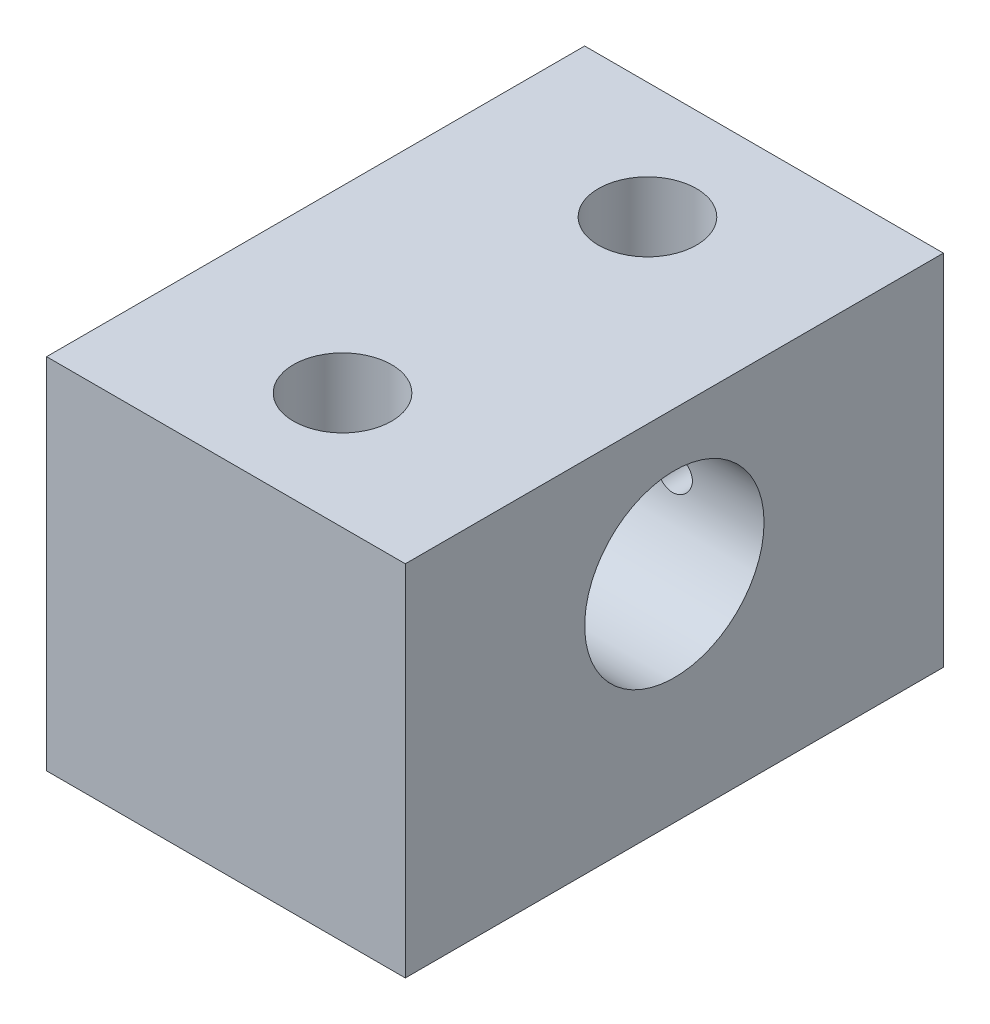
SolidWorks part; units mm, degrees
material "6061-T6 (SS)"
ref_plane "Front Plane" through (0, 0, 0) normal (0, 0, 1) x (1, 0, 0)
ref_plane "Top Plane" through (0, 0, 0) normal (0, 1, 0) x (1, 0, 0)
ref_plane "Right Plane" through (0, 0, 0) normal (1, 0, 0) x (0, 0, -1)
sketch "Sketch1" plane through (0, 0, 0) normal (0, 0, 1) x (1, 0, 0)
  line L1 (-25.4, -25.4) -> (25.4, -25.4)
  line L2 (-25.4, -25.4) -> (-25.4, 25.4)
  line L3 (-25.4, 25.4) -> (25.4, 25.4)
  line L4 (25.4, -25.4) -> (25.4, 25.4)
  line L5 (-25.4, -25.4) -> (25.4, 25.4) construction
  line L6 (-25.4, 25.4) -> (25.4, -25.4) construction
  point P0 (0, 0)
  dimension "D1" = 50.8
  dimension "D2" = 50.8
extrude "Extrude1" add sketch "Sketch1" along normal mid plane 76.2
sketch "Sketch2" plane through (25.4, 0, 0) normal (1, 0, 0) x (0, 0, -1)
  line L0 (38.1, 5.08) -> (0, 5.08) construction
  line L1 (-38.1, -25.4) -> (38.1, -25.4) construction
  line L2 (38.1, -25.4) -> (38.1, 25.4) construction
  line L3 (0, 27.94) -> (0, -27.94) construction
  circle A0 centre (0, 5.08) radius 12.7
  dimension "D2" = 25.4
  dimension "D3" = 30.48
extrude "Extrude2" cut sketch "Sketch2" against normal through all
sketch "Sketch3" plane through (0, 25.4, 0) normal (0, 1, 0) x (1, 0, 0)
  line L0 (0, 38.1) -> (0, -21.59) construction
  line L1 (25.4, 38.1) -> (-25.4, 38.1) construction
  line L2 (0, -21.59) -> (0, -38.1) construction
  line L3 (25.4, -38.1) -> (-25.4, -38.1) construction
  dimension "D1" = 16.51
hole_wizard "1/2 Clearance Hole1" positions "3DSketch1" profile "Sketch5" hole size "1/2" standard "Ansi Inch" end condition through all
sketch3d "3DSketch1"
  point P0 (0, 25.4, 21.59)
sketch "Sketch5" plane through (0, 25.4, 21.59) normal (1, 0, 0) x (0, 0, 1)
  line L0 (0, 0) -> (0, 50.8)
  line L1 (0, 50.8) -> (6.9456, 50.8)
  line L2 (6.9456, 50.8) -> (6.9456, 0)
  line L5 (6.9456, 0) -> (0, 0)
  line L11 (0, -6.35) -> (0, 107.95) construction
  dimension "Thru Hole Dia." = 13.8913
  dimension "Thru Hole Depth" = 50.8
mirror "Mirror1" about plane through (0, 0, 0) normal (0, 0, 1) of "1/2 Clearance Hole1"
sketch "Sketch6" plane through (0, 0, -38.1) normal (0, 0, -1) x (-1, 0, 0)
  line L0 (-12.7, -25.4) -> (-12.7, 5.08) construction
  line L1 (25.4, -25.4) -> (-25.4, -25.4) construction
  line L2 (-25.4, -25.4) -> (-25.4, 25.4) construction
  dimension "D1" = 30.48
  dimension "D2" = 12.7
hole_wizard "1/4-20 Tapped Hole1" positions "3DSketch2" profile "Sketch7" tap size "1/4-20" standard "Ansi Inch"
sketch3d "3DSketch2"
  point P0 (12.7, 5.08, -38.1)
sketch "Sketch7" plane through (12.7, 5.08, -38.1) normal (1, 0, 0) x (0, 1, 0)
  line L0 (0, 0) -> (0, 76.2)
  line L1 (0, 76.2) -> (2.5527, 76.2)
  line L2 (2.5527, 76.2) -> (2.5527, 0)
  line L5 (2.5527, 0) -> (0, 0)
  line L11 (0, -6.35) -> (0, 107.95) construction
  dimension "Thru Tap Drill Dia." = 5.1054
  dimension "Thru Tap Drill Depth" = 76.2
cosmetic thread "Hole Thread1" parameters "D2"=6.35
mirror "Mirror2" about plane through (0, 0, 0) normal (1, 0, 0) of "1/4-20 Tapped Hole1"
